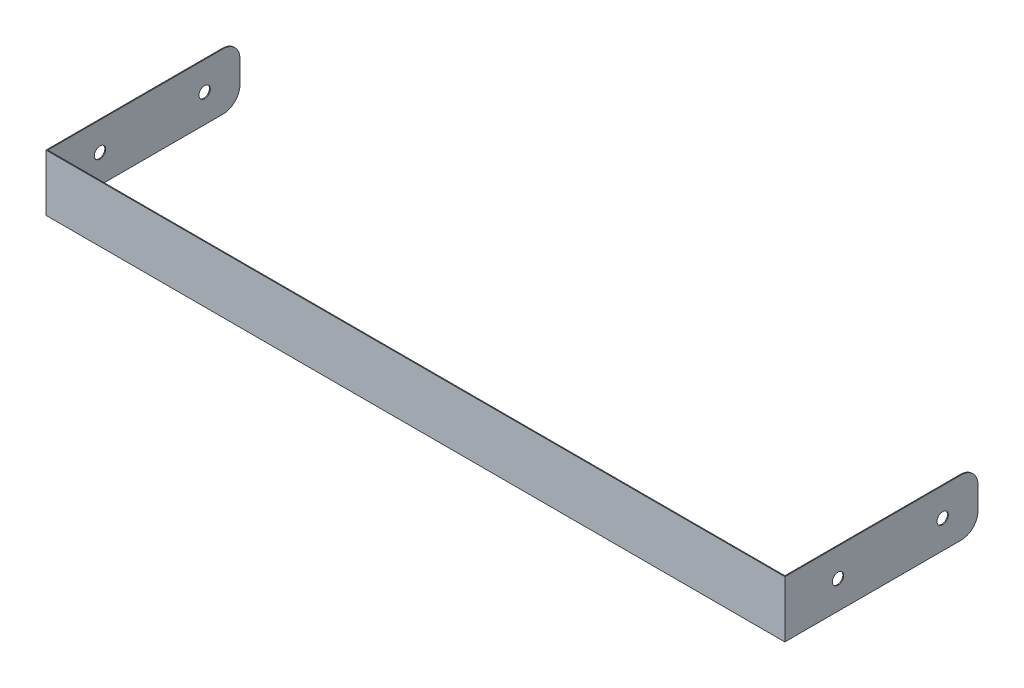
SolidWorks part; units mm, degrees
ref_plane "Front" through (0, 0, 0) normal (0, 0, 1) x (1, 0, 0)
ref_plane "Top" through (0, 0, 0) normal (0, 1, 0) x (1, 0, 0)
ref_plane "Right" through (0, 0, 0) normal (1, 0, 0) x (0, 0, -1)
sketch "Sketch1" plane through (0, 0, 0) normal (0, 1, 0) x (1, 0, 0)
  line L0 (0, 0) -> (0, -34.15)
  line L1 (0, -34.15) -> (-130.65, -34.15)
  line L2 (-130.65, -34.15) -> (-130.65, 0)
  line L3 (-130.5, 0) -> (-130.5, -34)
  line L4 (-130.5, -34) -> (-0.15, -34)
  line L5 (-0.15, -34) -> (-0.15, 0)
  line L6 (-0.15, 0) -> (0, 0)
  line L7 (-130.5, 0) -> (-130.65, 0)
  line L8 (-65.325, -34) -> (-65.325, -34.15)
  dimension "D1" = 130.35
  dimension "D2" = 34
  dimension "D3" = 0.15
extrude "Boss-Extrude1" add sketch "Sketch1" along normal blind 10 contours L4 L5 L6 L0 L1 L2 L7 L3
fillet "Fillet1" radius 3 4 edges at (-0.075, 0, 0) (-0.075, 10, 0) (-130.575, 0, 0) (-130.575, 10, 0)
sketch "Sketch2" plane through (0, 0, 0) normal (1, 0, 0) x (0, 0, -1)
  line L0 (0, 5) -> (-6.25, 5)
  line L1 (-6.25, 5) -> (-24.75, 5)
  line L4 (-34.15, 0) -> (-3, 0)
  line L5 (0, 3) -> (0, 7)
  line L6 (-3, 10) -> (-34.15, 10)
  line L7 (-34.15, 10) -> (-34.15, 0)
  line L8 (-34.15, 0) -> (-3, 0)
  line L9 (0, 3) -> (0, 7)
  line L10 (-3, 10) -> (-34.15, 10)
  line L11 (-34.15, 10) -> (-34.15, 0)
  circle A0 centre (-6.25, 5) radius 1
  circle A1 centre (-24.75, 5) radius 1
  arc A2 (-3, 0) -> (0, 3) centre (-3, 3) ccw
  arc A3 (0, 7) -> (-3, 10) centre (-3, 7) ccw
  arc A4 (-3, 0) -> (0, 3) centre (-3, 3) ccw
  arc A5 (0, 7) -> (-3, 10) centre (-3, 7) ccw
  dimension "D2" = 6.25
  dimension "D3" = 18.5
  dimension "D1" = 0
extrude "Cut-Extrude1" cut sketch "Sketch2" against normal up to surface (130.65 mm away) contours A0 | A1 up to face at (-130.65, 5, 12.1762)
